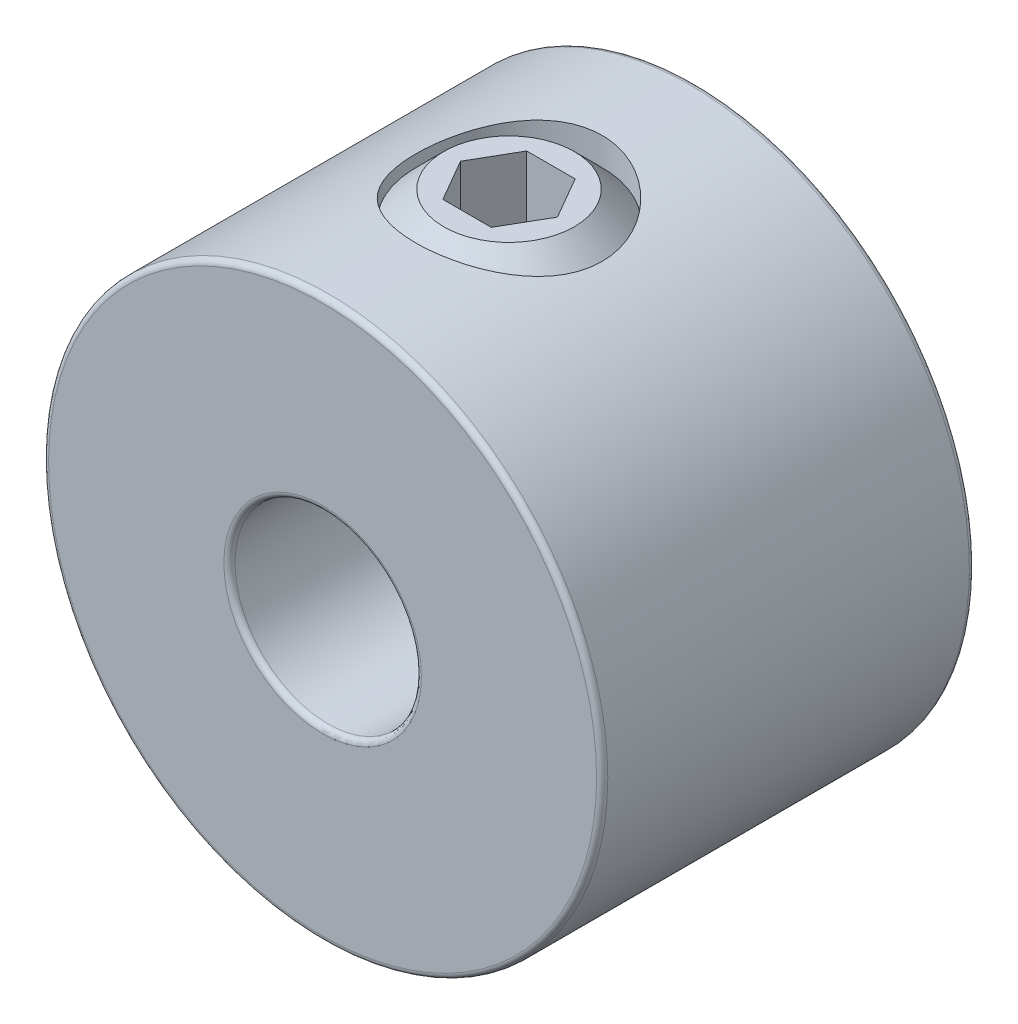
SolidWorks part; units mm, degrees
ref_plane "Front Plane" through (0, 0, 0) normal (0, 0, 1) x (1, 0, 0)
ref_plane "Top Plane" through (0, 0, 0) normal (0, 1, 0) x (1, 0, 0)
ref_plane "Right Plane" through (0, 0, 0) normal (1, 0, 0) x (0, 0, -1)
sketch "Sketch1" plane through (0, 0, 0) normal (0, 0, 1) x (1, 0, 0)
  circle A0 centre (0, 0) radius 3
  circle A1 centre (0, 0) radius 1
  point P4 (3, 0)
  point P5 (0, 3)
  dimension "Bore Dia" = 2
  dimension "OD" = 6
extrude "Extrude1" add sketch "Sketch1" along normal blind 4
ref_plane "Plane1" through (0, 3, 0) normal (0, 1, 0) x (-1, 0, 0)
sketch "Sketch2" plane through (0, 3, 0) normal (0, 1, 0) x (-1, 0, 0)
  line L0 (0, 0) -> (0, 4) construction
  line L2 (3, 4) -> (-3, 4) construction
  circle A0 centre (0, 2) radius 1
  dimension "Set Screw Dia" = 2
extrude "Cut-Extrude1" cut sketch "Sketch2" against normal up to surface (3 mm away) up to plane "Top Plane"
ref_plane "Plane2" through (0, 0, 2) normal (0, 0, 1) x (1, 0, 0)
sketch "Sketch3" plane through (0, 0, 2) normal (0, 0, 1) x (1, 0, 0)
  line L0 (-0.7, 3) -> (-1, 2.7)
  line L1 (0, 0) -> (0, 3)
  line L2 (0, 0) -> (-0.7, 0)
  line L3 (-1, 0.3) -> (-1, 2.7)
  line L4 (0, 3) -> (-0.7, 3)
  line L5 (0, 0) -> (0, -3.5) construction
  line L6 (-1, 2.7) -> (0, 2.7) construction
  line L8 (-0.7, 0) -> (-1, 0.3)
  dimension "D1" = 2
  dimension "Screw Length" = 3
  dimension "D2" = 45
  dimension "D3" = 0.3
  dimension "D4" = 45
  dimension "D7" = 1
revolve "Revolve1" add sketch "Sketch3" angle 360 about L1
sketch "Sketch4" plane through (0, 3, 0) normal (0, 1, 0) x (0, 0, -1)
  line L0 (-2, 0.5196) -> (-2, -0.5196) construction
  line L1 (-2, 0.5196) -> (-2.45, 0.2598)
  line L2 (-2.45, 0.2598) -> (-2.45, -0.2598)
  line L3 (-2.45, -0.2598) -> (-2, -0.5196)
  line L4 (-2, -0.5196) -> (-1.55, -0.2598)
  line L5 (-1.55, -0.2598) -> (-1.55, 0.2598)
  line L6 (-1.55, 0.2598) -> (-2, 0.5196)
  circle A0 centre (-2, 0) radius 0.45 construction
  circle A1 centre (-2, 0) radius 0.5196 construction
  dimension "D1" = 1.0392
  dimension "Hex" = 0.9
extrude "Cut-Extrude2" cut sketch "Sketch4" against normal blind 0.72
fillet "Fillet1" radius 0.06 4 edges at (1, 0, 0) (1, 0, 4) (3, 0, 0) (3, 0, 4)
equation "\"D1@Fillet1\" = \"OD@Sketch1\"*.01"
equation "\"D1@Cut-Extrude2\" = \"Hex@Sketch4\"*.8"
